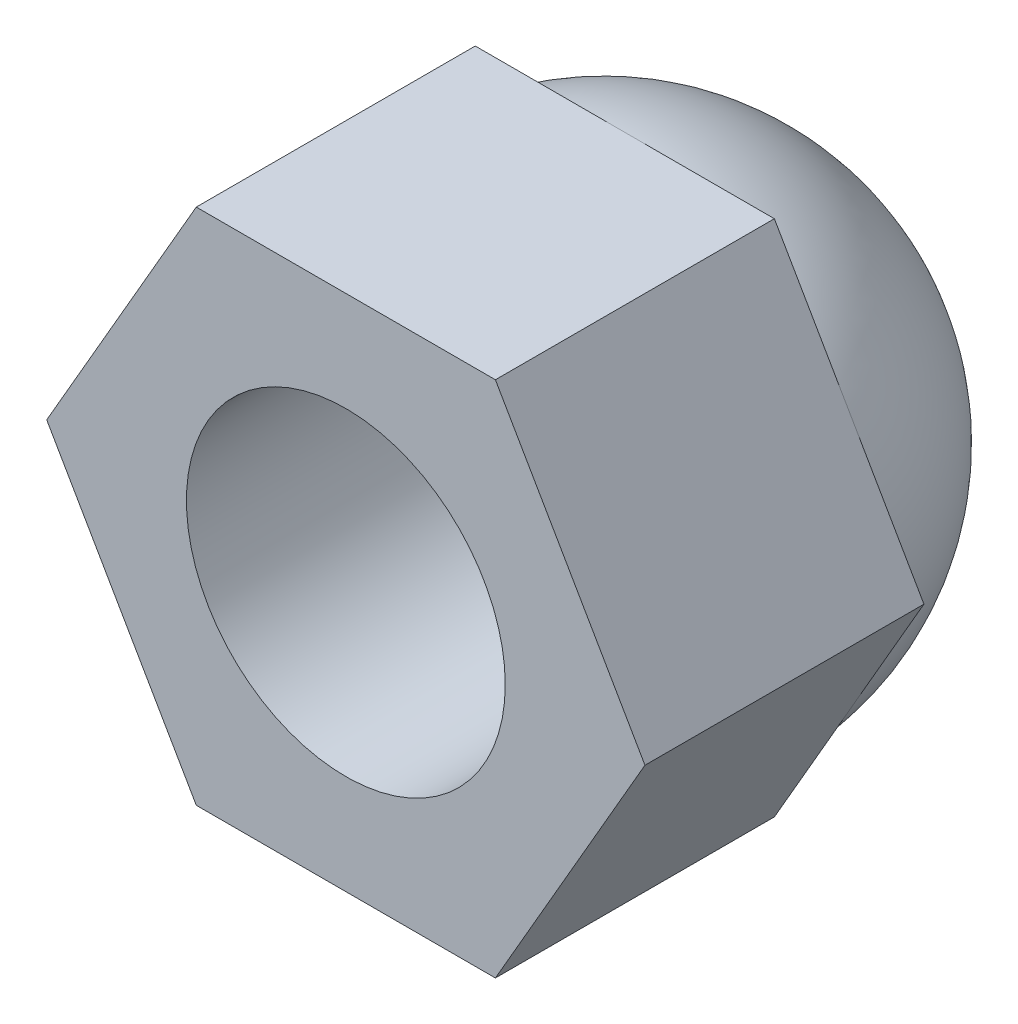
SolidWorks part; units mm, degrees
ref_plane "Alzado" through (0, 0, 0) normal (0, 0, 1) x (1, 0, 0)
ref_plane "Planta" through (0, 0, 0) normal (0, 1, 0) x (1, 0, 0)
ref_plane "Vista lateral" through (0, 0, 0) normal (1, 0, 0) x (0, 0, -1)
sketch "Croquis1" plane through (0, 0, 0) normal (0, 0, 1) x (1, 0, 0)
  line L1 (7.5056, 0) -> (3.7528, 6.5)
  line L2 (3.7528, 6.5) -> (-3.7528, 6.5)
  line L3 (-3.7528, 6.5) -> (-7.5056, 0)
  line L4 (-7.5056, 0) -> (-3.7528, -6.5)
  line L5 (-3.7528, -6.5) -> (3.7528, -6.5)
  line L6 (3.7528, -6.5) -> (7.5056, 0)
  circle A0 centre (0, 0) radius 6.5 construction
  dimension "D1" = 13
extrude "Saliente-Extruir1" add sketch "Croquis1" along normal blind 7
sketch "Croquis2" plane through (0, 0, 0) normal (1, 0, 0) x (0, 0, -1)
  line L0 (0, 0) -> (6, 0)
  line L1 (0, 0) -> (0, -6.5)
  arc A0 (6, 0) -> (0, -6.5) centre (-0.5208, 0) cw
  dimension "D1" = 6
revolve "Revolución1" add sketch "Croquis2" angle 360 about L0
sketch "Croquis3" plane through (0, 0, 7) normal (0, 0, 1) x (1, 0, 0)
  circle A0 centre (0, 0) radius 4
  dimension "D1" = 8
extrude "Cortar-Extruir1" cut sketch "Croquis3" against normal blind 7
